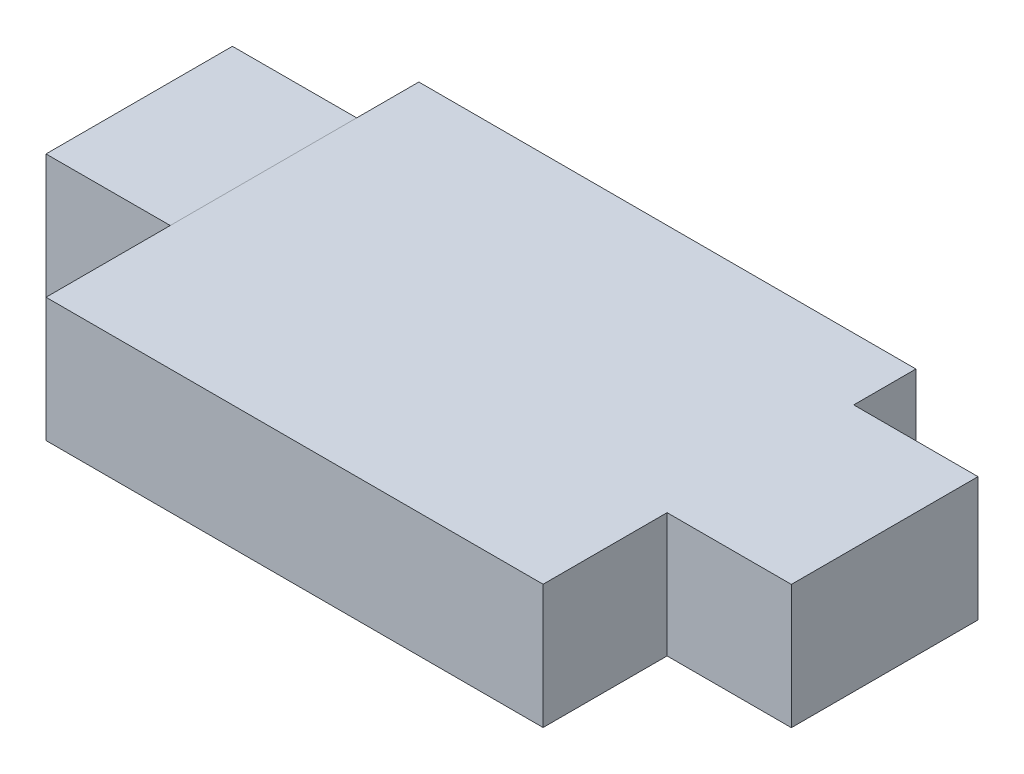
SolidWorks part; units mm, degrees
material "Stal węglowa"
ref_plane "Płaszczyzna przednia" through (0, 0, 0) normal (0, 0, 1) x (1, 0, 0)
ref_plane "Płaszczyzna górna" through (0, 0, 0) normal (0, 1, 0) x (1, 0, 0)
ref_plane "Płaszczyzna prawa" through (0, 0, 0) normal (1, 0, 0) x (0, 0, -1)
sketch "Szkic1" plane through (0, 0, 0) normal (0, 0, 1) x (1, 0, 0)
  line L0 (0, -199.087) -> (0, -197.0896)
  line L1 (-7.9976, -199.087) -> (-8, -197.0896)
  line L15 (-0.3835, -201.5501) -> (-22.0503, -205.8858)
  line L16 (-21.9059, -207.8803) -> (0.2631, -203.4442)
  line L17 (1.9596, -201.1319) -> (2.0038, -199.1312)
  line L18 (2.0038, -199.1312) -> (2.0038, -185.1324)
  line L19 (2.0038, -185.1324) -> (0, -185.0881)
  line L20 (0, -185.0881) -> (0, -197.0896)
  line L21 (0, -197.0896) -> (-8, -197.0896)
  line L22 (-8, -197.0896) -> (-8, -185.0874)
  line L23 (-8, -185.0874) -> (-9.9976, -185.0874)
  line L24 (-9.9976, -185.0874) -> (-9.9976, -199.5844)
  line L25 (-10.3266, -200.0543) -> (-23.157, -201.7973)
  line L26 (-22.5044, -203.6809) -> (-9.6426, -201.9337)
  line L27 (-7.9976, -199.5844) -> (-7.9976, -199.087)
  line L28 (-7.9976, -199.087) -> (0, -199.087)
  line L29 (0, -199.087) -> (-0.0442, -201.0877)
  line L36 (0, -197.0896) -> (-8, -197.0896)
  line L43 (-7.9976, -199.087) -> (0, -199.087)
  arc A4 (0.2631, -203.4442) -> (1.9596, -201.1319) centre (-0.5398, -201.0767) ccw
  arc A5 (-10.3266, -200.0543) -> (-9.9976, -199.5844) centre (-10.4976, -199.5844) ccw
  arc A6 (-9.6426, -201.9337) -> (-7.9976, -199.5844) centre (-10.4976, -199.5844) ccw
  arc A7 (-0.3835, -201.5501) -> (-0.0442, -201.0877) centre (-0.5441, -201.0766) ccw
  spline S2 degree 3 poles (628.9418, -964.9702) (-843.3951, 554.1785) (884.1696, -811.2244) (-952.6248, 157.8402) knots -60.982435 -60.982435 -60.982435 -60.982435 51.631883 51.631883 51.631883 51.631883 only from (-22.0503, -205.8858) to (-21.9059, -207.8803)
  spline S3 degree 3 poles (483.8857, -1063.7178) (-806.2054, 584.367) (897.0656, -776.8328) (-980.8895, 81.7942) knots -65.394929 -65.394929 -65.394929 -65.394929 56.844745 56.844745 56.844745 56.844745 only from (-23.157, -201.7973) to (-22.5044, -203.6809)
  dimension "D1" = 0
extrude "Dodanie-wyciągnięcie1" add sketch "Szkic1" against normal blind 6 contours L43 L0 L36 L1
sketch "Szkic2" plane through (0, 0, 0) normal (1, 0, 0) x (0, 0, -1)
  line L2 (6, -199.087) -> (0, -199.087) construction
  line L3 (6, -197.0896) -> (0, -197.0896) construction
  line L4 (1.9955, -199.087) -> (4.9991, -199.087)
  line L5 (1.9955, -199.087) -> (1.9955, -197.0896)
  line L6 (1.9955, -197.0896) -> (4.9991, -197.0896)
  line L7 (4.9991, -199.087) -> (4.9991, -197.0896)
extrude "Dodanie-wyciągnięcie2" add sketch "Szkic2" along normal blind 2
sketch "Szkic3" plane through (-8.2348, -0.0098, 0) normal (-1, -0.0012, 0) x (0, 0, 1)
  line L1 (-6, -199.0773) -> (0, -199.0773) construction
  line L2 (-6, -197.0799) -> (0, -197.0799) construction
  line L3 (-1.9998, -199.0773) -> (-5, -199.0773)
  line L4 (-1.9998, -199.0773) -> (-1.9998, -197.0799)
  line L5 (-1.9998, -197.0799) -> (-5, -197.0799)
  line L6 (-5, -199.0773) -> (-5, -197.0799)
extrude "Dodanie-wyciągnięcie3" add sketch "Szkic3" along normal blind 2
